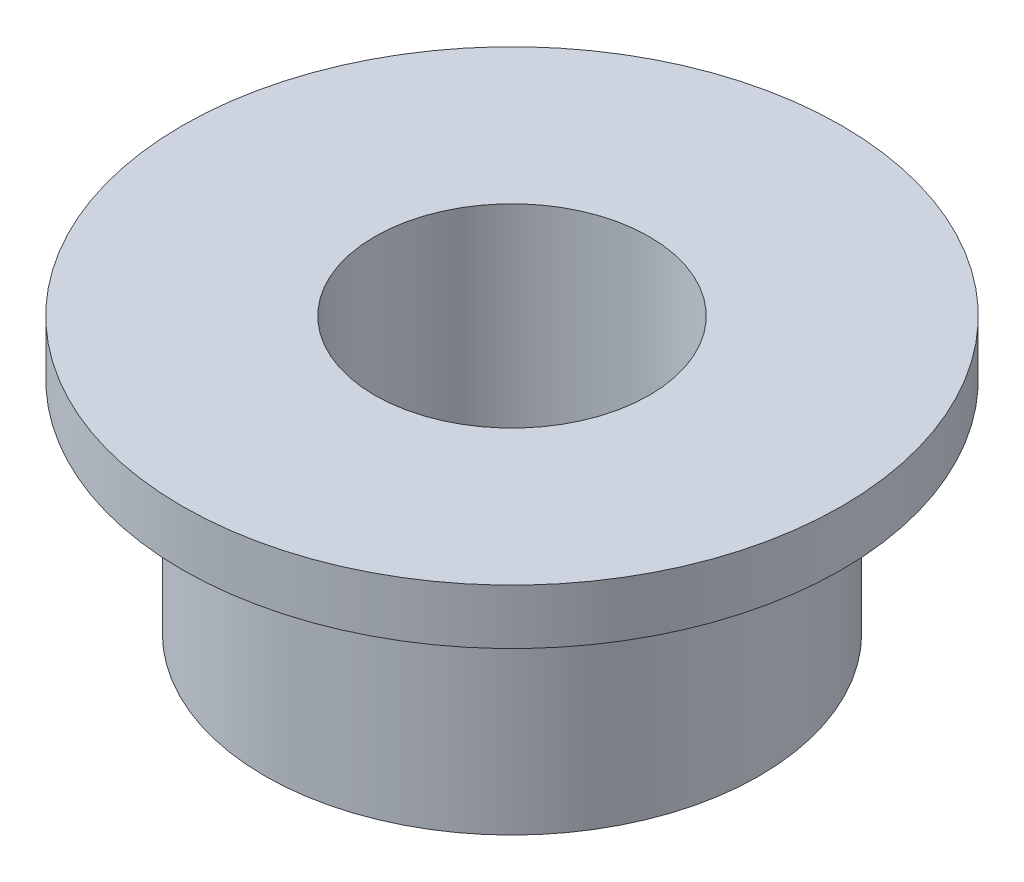
SolidWorks part; units mm, degrees
ref_plane "Front Plane" through (0, 0, 0) normal (0, 0, 1) x (1, 0, 0)
ref_plane "Top Plane" through (0, 0, 0) normal (0, 1, 0) x (1, 0, 0)
ref_plane "Right Plane" through (0, 0, 0) normal (1, 0, 0) x (0, 0, -1)
sketch "Sketch1" plane through (0, 0, 0) normal (1, 0, 0) x (0, 0, -1)
  line L0 (25, 0) -> (25, 50)
  line L1 (25, 50) -> (60, 50)
  line L2 (60, 50) -> (60, 40)
  line L3 (60, 40) -> (45, 40)
  line L4 (45, 40) -> (45, 0)
  line L5 (45, 0) -> (25, 0)
  line L6 (0, 0) -> (25, 0) construction
  line L7 (0, 0) -> (0, 28.34) construction
  dimension "D1" = 20
  dimension "D2" = 25
  dimension "D3" = 35
  dimension "D4" = 40
  dimension "D5" = 50
  dimension "D6" = 28.34
revolve "Revolve1" add sketch "Sketch1" angle 360 about L7
